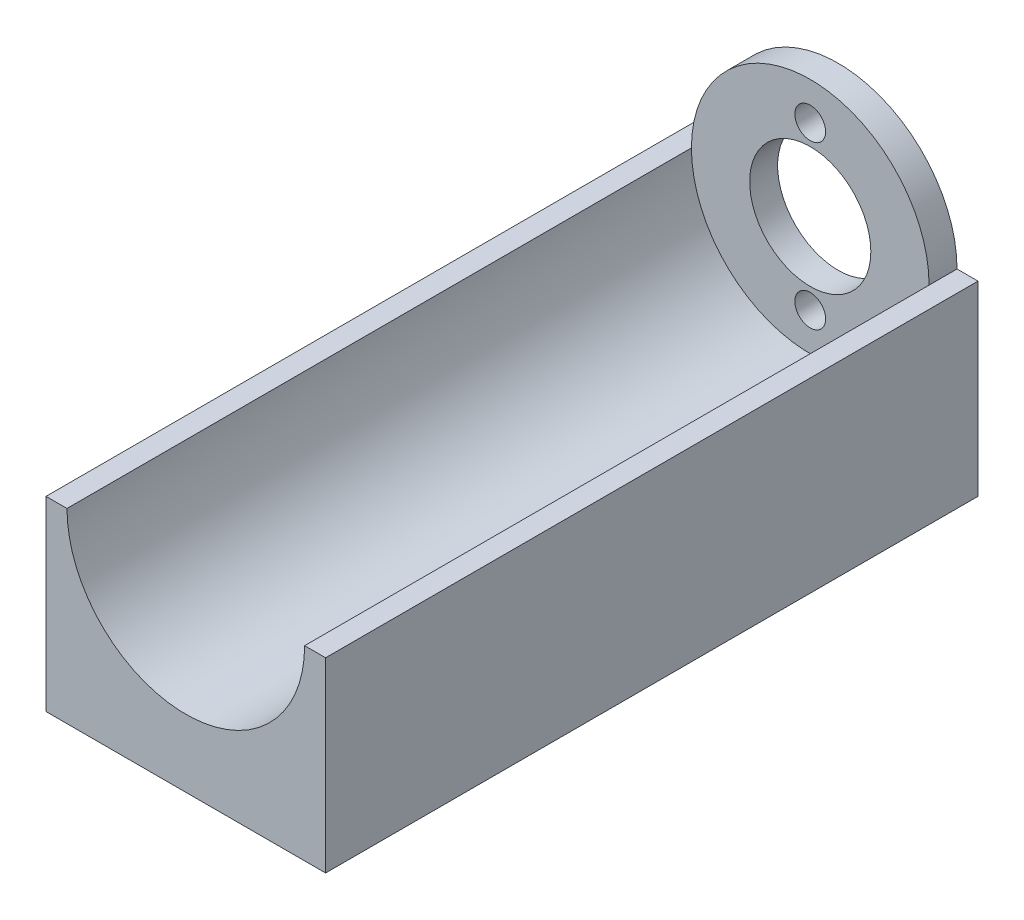
SolidWorks part; units mm, degrees
ref_plane "Front Plane" through (0, 0, 0) normal (0, 0, 1) x (1, 0, 0)
ref_plane "Top Plane" through (0, 0, 0) normal (0, 1, 0) x (1, 0, 0)
ref_plane "Right Plane" through (0, 0, 0) normal (1, 0, 0) x (0, 0, -1)
sketch "Sketch1" plane through (0, 0, 0) normal (0, 0, 1) x (1, 0, 0)
  circle A0 centre (0, 0) radius 12.75
  circle A1 centre (0, 0) radius 6.5
  dimension "D1" = 25.5
  dimension "D2" = 13
extrude "Boss-Extrude1" add sketch "Sketch1" along normal blind 3
sketch "Sketch2" plane through (0, 0, 3) normal (0, 0, 1) x (1, 0, 0)
  line L0 (-15, 0) -> (-15, 50000) construction
  line L1 (15, -6.7646) -> (15, 49993.2354) construction
  line L2 (0, -20) -> (50000, -20) construction
  line L3 (15, 0) -> (15, -20)
  line L4 (15, -20) -> (-15, -20)
  line L5 (-15, -20) -> (-15, 0)
  line L6 (-15, 0) -> (-12.75, 0)
  line L7 (15, 0) -> (12.75, 0)
  circle A3 centre (0, 0) radius 12.75 construction
  circle A4 centre (0, 0) radius 12.75
  circle M4 centre (0, 0) radius 12.75
  dimension "D1" = 20
  dimension "D2" = 15
  dimension "D3" = 15
extrude "Boss-Extrude2" add sketch "Sketch2" along normal blind 67 and the other way up to surface (3 mm away) contours L5 L4 L3 M4
sketch "Sketch4" plane through (0, -20, 0) normal (0, -1, 0) x (1, 0, 0)
  line L1 (15, 70) -> (-15, 70) construction
  line L2 (-10, 67) -> (10, 67) construction
  circle A0 centre (-10, 67) radius 2.515
  point P2 (0, 70)
  point P3 (0, 67)
  dimension "D1" = 5.03
  dimension "D3" = 3
  dimension "D4" = 20
extrude "Cut-Extrude1" cut sketch "Sketch4" against normal blind 6
pattern_linear "LPattern1" count 2 spacing 20 along (1, 0, 0) count 7 spacing 10 along (0, 0, -1) of "Cut-Extrude1"
sketch "Sketch5" plane through (0, 0, 0) normal (0, 0, -1) x (-1, 0, 0)
  line L0 (0, 0) -> (0, 50000) construction
  line L1 (-22.8857, 0) -> (22.8857, 0) construction
  circle A0 centre (0, 8.7) radius 1.65
  circle A1 centre (0, -8.7) radius 1.65
  point P5 (0, 0)
  dimension "D2" = 3.3
  dimension "D1" = 8.7
extrude "Cut-Extrude2" cut sketch "Sketch5" against normal blind 75
hole_wizard "CBORE for M3 Pan Head Machine Screw1" [suppressed] positions "Sketch6" profile "Sketch8" counterbore size "M3" standard "ANSI Metric"
sketch "Sketch6" plane through (0, -20, 0) normal (0, -1, 0) x (-1, 0, 0)
  point P0 (-9.9912, -4.9824)
sketch "Sketch8" plane through (9.9912, -20, 4.9824) normal (1, 0, 0) x (0, 0, -1)
  line L0 (0, 0) -> (0, 8.0215)
  line L1 (0, 8.0215) -> (1.7, 7)
  line L2 (1.7, 7) -> (1.7, 2.4)
  line L3 (1.7, 2.4) -> (3.5, 2.4)
  line L4 (3.5, 2.4) -> (3.5, 0)
  line L5 (3.5, 0) -> (0, 0)
  line L10 (0, 8.0215) -> (-1.7, 7) construction
  line L11 (0, -6.35) -> (0, 107.95) construction
  dimension "Hole Dia." = 3.4
  dimension "Hole Depth" = 7
  dimension "C'Bore Dia." = 7
  dimension "C'Bore Depth" = 2.4
  dimension "Drill Angle" = 118
pattern_linear "LPattern2" [suppressed] count 2 spacing 20 count 4 spacing 20
